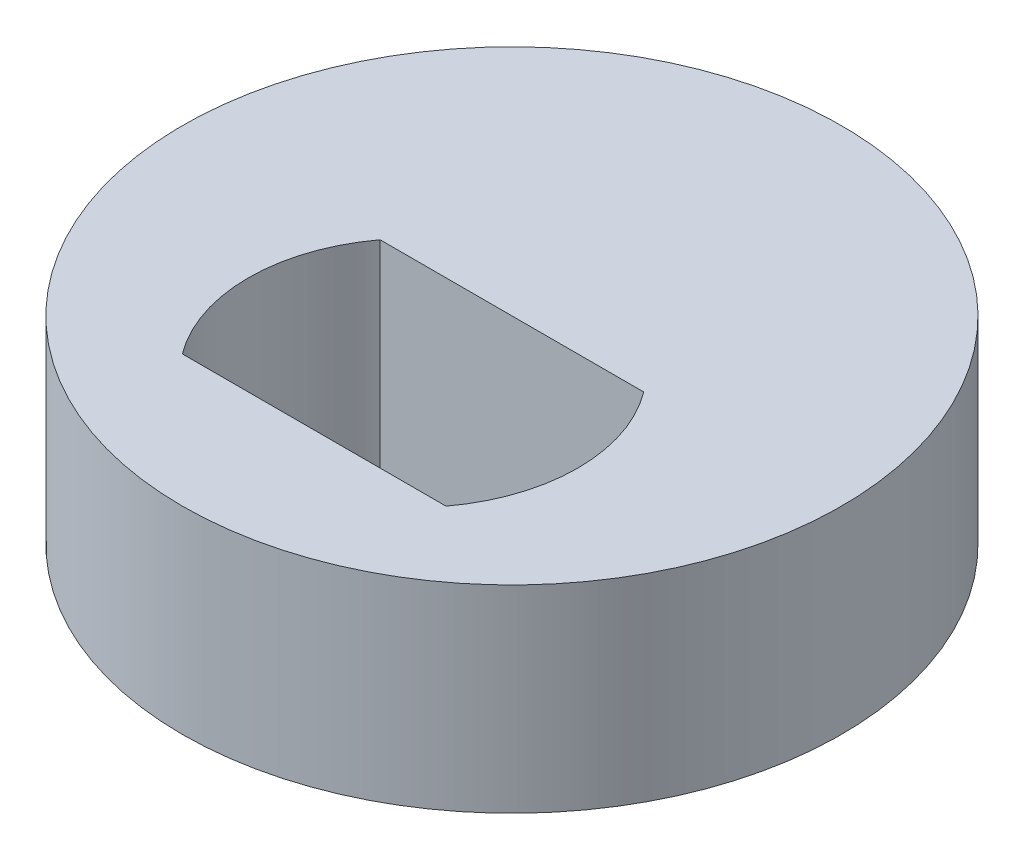
SolidWorks part; units mm, degrees
ref_plane "Front Plane" through (0, 0, 0) normal (0, 0, 1) x (1, 0, 0)
ref_plane "Top Plane" through (0, 0, 0) normal (0, 1, 0) x (1, 0, 0)
ref_plane "Right Plane" through (0, 0, 0) normal (1, 0, 0) x (0, 0, -1)
sketch "Sketch1" plane through (0, 0, 0) normal (0, 1, 0) x (1, 0, 0)
  line L1 (-2, 0) -> (2, 0)
  line L2 (-2, -3) -> (2, -3)
  circle A0 centre (0, 0) radius 5
  arc A2 (-2, 0) -> (-2, -3) centre (0, -1.5) ccw
  arc A3 (2, -3) -> (2, 0) centre (0, -1.5) ccw
  dimension "D1" = 10
  dimension "D3" = 5
  dimension "D2" = 1.5
  dimension "D4" = 4
extrude "Boss-Extrude1" add sketch "Sketch1" along normal blind 3
